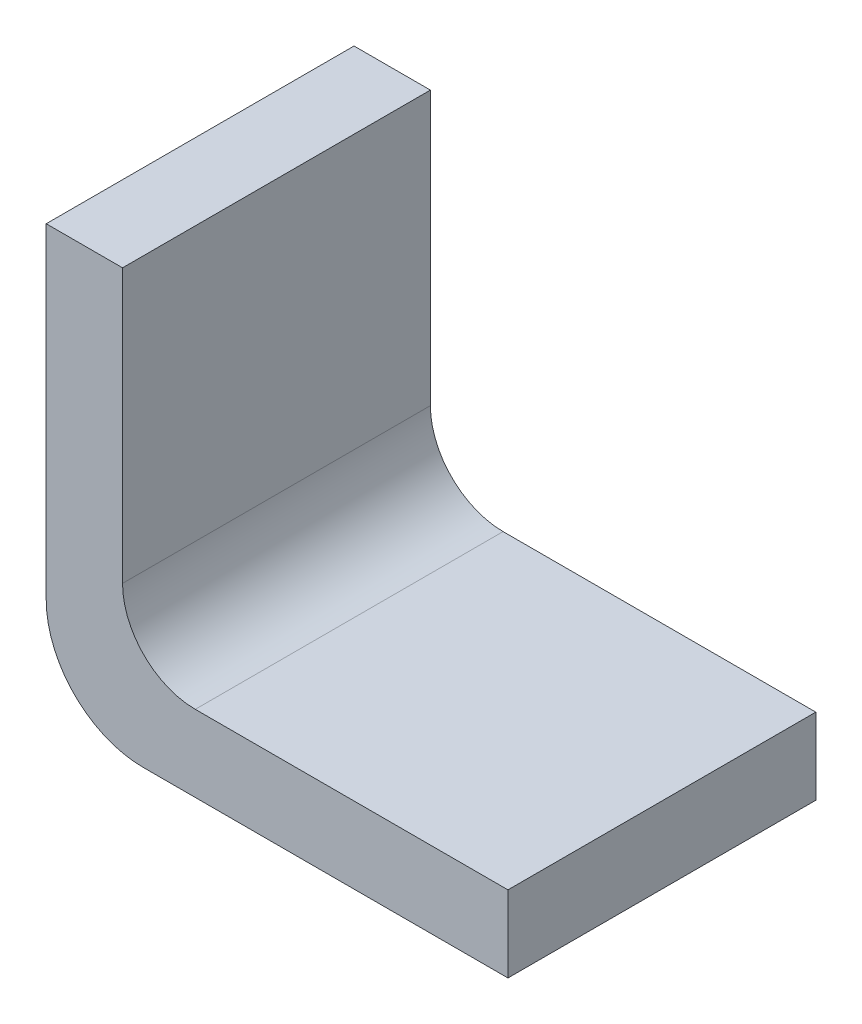
SolidWorks part; units mm, degrees
ref_plane "Front Plane" through (0, 0, 0) normal (0, 0, 1) x (1, 0, 0)
ref_plane "Top Plane" through (0, 0, 0) normal (0, 1, 0) x (1, 0, 0)
ref_plane "Right Plane" through (0, 0, 0) normal (1, 0, 0) x (0, 0, -1)
sketch "Sketch1" plane through (0, 0, 0) normal (0, 0, 1) x (1, 0, 0)
  line L0 (0, 2) -> (0, 8.7122)
  line L1 (0, 8.7122) -> (1.5748, 8.7122)
  line L2 (1.5748, 8.7122) -> (1.5748, 3.0748)
  line L3 (3.0748, 1.5748) -> (9.525, 1.5748)
  line L4 (9.525, 1.5748) -> (9.525, 0)
  line L5 (9.525, 0) -> (2, 0)
  arc A0 (0, 2) -> (2, 0) centre (2, 2) ccw
  arc A1 (3.0748, 1.5748) -> (1.5748, 3.0748) centre (3.0748, 3.0748) cw
  point P9 (0, 0)
  dimension "D4" = 2
  dimension "D5" = 1.5
  dimension "D1" = 1.5748
  dimension "D2" = 9.525
  dimension "D3" = 8.7122
extrude "Boss-Extrude1" add sketch "Sketch1" along normal blind 6.35
